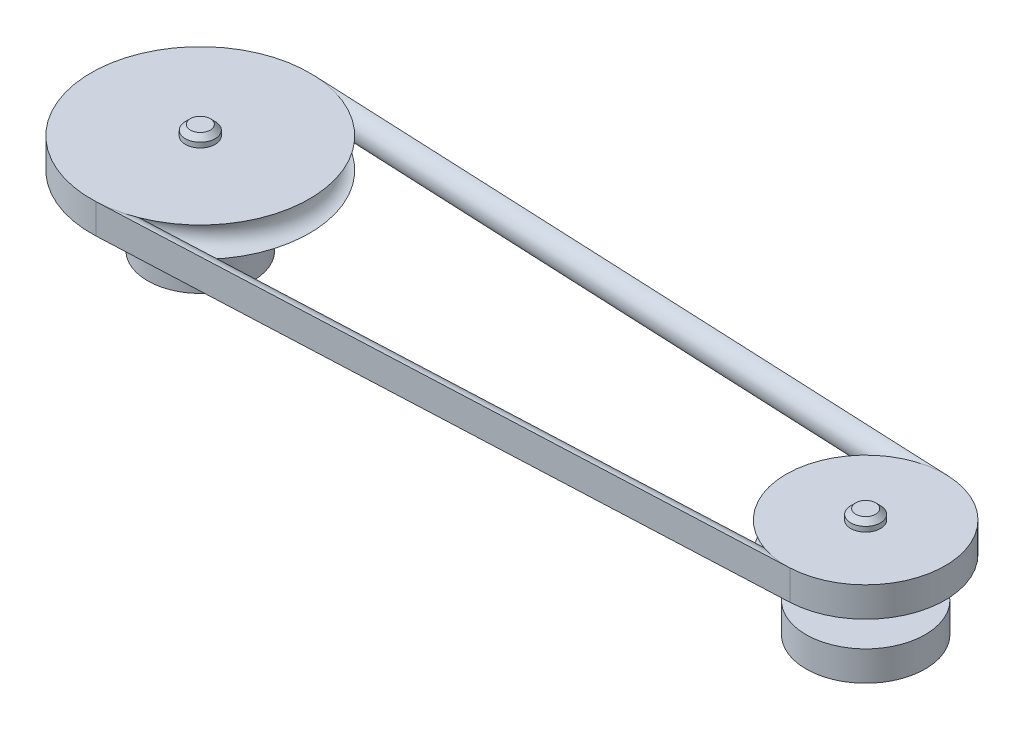
SolidWorks part; units mm, degrees
ref_plane "Front Plane" through (0, 0, 0) normal (0, 0, 1) x (1, 0, 0)
ref_plane "Top Plane" through (0, 0, 0) normal (0, 1, 0) x (1, 0, 0)
ref_plane "Right Plane" through (0, 0, 0) normal (1, 0, 0) x (0, 0, -1)
sketch "Sketch1" plane through (0, 0, 0) normal (0, 1, 0) x (1, 0, 0)
  line L0 (0, 0) -> (0, 223.5) construction
  circle A0 centre (-167.5, 0) radius 26.5
  circle A1 centre (167.5, 0) radius 30
  dimension "D1" = 53
  dimension "D2" = 60
  dimension "D3" = 335
  dimension "D4" = 167.5
extrude "Boss-Extrude1" add sketch "Sketch1" along normal blind 15 contours A1 | A0
sketch "Sketch2" plane through (0, 15, 0) normal (0, 1, 0) x (1, 0, 0)
  circle A0 centre (-167.5, 0) radius 7.5
  circle A1 centre (167.5, 0) radius 7.5
  dimension "D1" = 15
  dimension "D2" = 15
extrude "Boss-Extrude2" add sketch "Sketch2" along normal blind 40
sketch "Sketch4" plane through (0, 0, 0) normal (0, 0, 1) x (1, 0, 0)
  line L0 (-167.5, 55) -> (-167.5, 27.9416) construction
  line L1 (-222.5, 50) -> (-167.5, 50)
  line L2 (-222.5, 50) -> (-222.5, 35)
  line L3 (-222.5, 35) -> (-167.5, 35)
  line L4 (-167.5, 50) -> (-167.5, 35)
  line L5 (-160, 55) -> (-175, 55) construction
  line L6 (-141, 15) -> (-194, 15) construction
  line L7 (167.5, 55) -> (167.5, 81.0352) construction
  line L8 (175, 55) -> (160, 55) construction
  line L9 (167.5, 55) -> (167.5, 15) construction
  dimension "D1" = 55
  dimension "D2" = 5
  dimension "D3" = 20
revolve "Revolve3" add sketch "Sketch4" angle 360 about L0
sketch "Sketch5" plane through (0, 0, 0) normal (0, 0, 1) x (1, 0, 0)
  line L0 (-222.5, 50) -> (-222.5, 35) construction
  circle A0 centre (-222.5, 42.5) radius 7.5
revolve "Cut-Revolve1" cut sketch "Sketch5" angle 360 about axis through (-167.5, 55, 0) along (0, 1, 0)
sketch "Sketch6" plane through (0, 0, 0) normal (0, 0, 1) x (1, 0, 0)
  line L0 (167.5, 55) -> (167.5, 105.4834) construction
  line L1 (175, 55) -> (160, 55) construction
  line L2 (167.5, 55) -> (167.5, 15) construction
  line L3 (197.5, 15) -> (137.5, 15) construction
  line L4 (167.5, 50) -> (127.5, 50)
  line L5 (167.5, 50) -> (167.5, 35)
  line L6 (167.5, 35) -> (127.5, 35)
  line L7 (127.5, 50) -> (127.5, 35)
  dimension "D1" = 5
  dimension "D2" = 20
  dimension "D3" = 40
revolve "Revolve4" add sketch "Sketch6" angle 360 about L0
sketch "Sketch7" plane through (0, 0, 0) normal (0, 0, 1) x (1, 0, 0)
  line L0 (127.5, 50) -> (127.5, 35) construction
  circle A0 centre (127.5, 42.5) radius 7.5
revolve "Cut-Revolve2" cut sketch "Sketch7" angle 360 about axis through (167.5, 55, 0) along (0, -1, 0)
ref_plane "Plane1" through (0, 42.5, 0) normal (0, 1, 0) x (1, 0, 0)
sketch "Sketch8" plane through (0, 42.5, 0) normal (0, 1, 0) x (1, 0, 0)
  line L0 (168.9552, 32.4674) -> (-165.3731, 47.4524)
  line L1 (-165.3731, -47.4524) -> (168.9552, -32.4674)
  circle A0 centre (-167.5, 0) radius 47.5 construction
  arc A1 (-165.3731, 47.4524) -> (-165.3731, -47.4524) centre (-167.5, 0) ccw
  circle A2 centre (167.5, 0) radius 32.5 construction
  arc A3 (168.9552, -32.4674) -> (168.9552, 32.4674) centre (167.5, 0) ccw
ref_plane "Plane2" through (-165.3731, 42.5, 47.4524) normal (0.999, 0, -0.0448) x (-0.0448, 0, -0.999)
sketch "Sketch9" plane through (-165.3731, 42.5, 47.4524) normal (0.999, 0, -0.0448) x (-0.0448, 0, -0.999)
  line L0 (-7.5, 7.5) -> (-7.5, -7.5)
  arc A0 (-7.5, 7.5) -> (-7.5, -7.5) centre (-7.5, 0) cw
sweep "Sweep1" add profiles "Sketch9" path "Sketch8"
chamfer "Chamfer1" distance 2.5 angle 45 2 edges at (167.5, 55, 7.5) (-167.5, 55, 7.5)
sketch "Sketch10" plane through (0, 0, 0) normal (0, -1, 0) x (1, 0, 0)
  circle A0 centre (-167.5, 0) radius 7.5
  dimension "D1" = 15
extrude "Cut-Extrude1" cut sketch "Sketch10" against normal blind 15
sketch "Sketch11" plane through (0, 0, 0) normal (0, -1, 0) x (1, 0, 0)
  circle A0 centre (167.5, 0) radius 7.5
  dimension "D1" = 15
extrude "Cut-Extrude2" cut sketch "Sketch11" against normal blind 15
